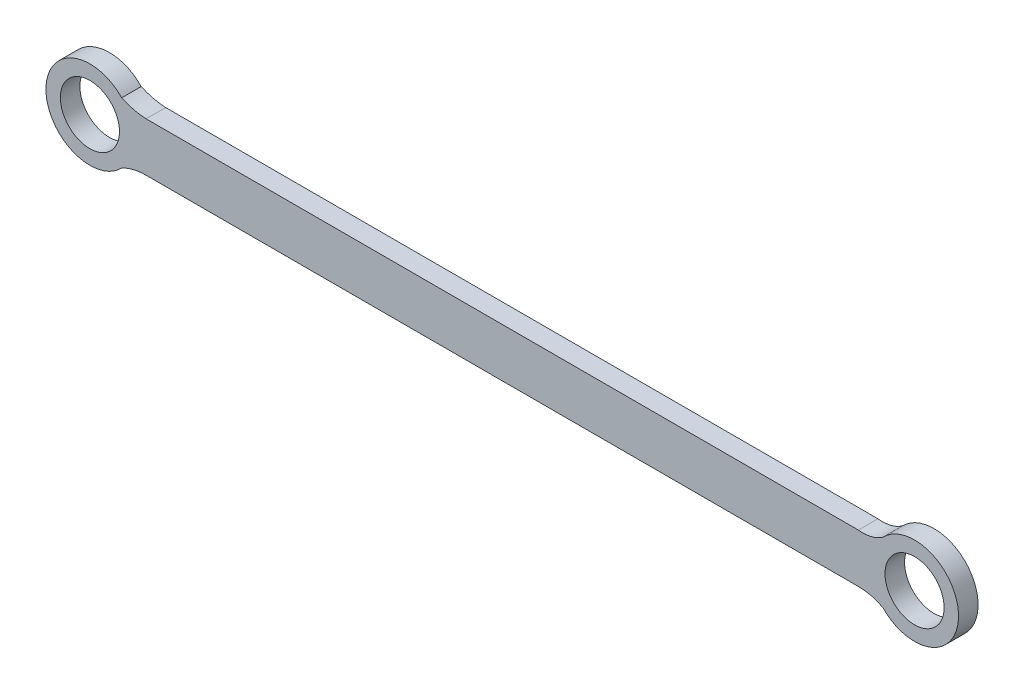
SolidWorks part; units mm, degrees
ref_plane "前视基准面" through (0, 0, 0) normal (0, 0, 1) x (1, 0, 0)
ref_plane "上视基准面" through (0, 0, 0) normal (0, 1, 0) x (1, 0, 0)
ref_plane "右视基准面" through (0, 0, 0) normal (1, 0, 0) x (0, 0, -1)
sketch "草图1" plane through (0, 0, 0) normal (0, 0, 1) x (1, 0, 0)
  line L0 (82, 4.5009) -> (-63.75, 4.5009)
  line L1 (-63.75, -5.4991) -> (82, -5.4991)
  line L2 (-141.9968, -0.4991) -> (145.6273, -0.4991) construction
  line L3 (0, 49.3748) -> (0, -44.6051) construction
  line L4 (93.4981, 49.3748) -> (93.4981, -44.6051) construction
  line L5 (-75.2519, 47.3518) -> (-75.2519, -43.3177) construction
  line L6 (82, 49.3748) -> (82, -47.6473) construction
  line L7 (-63.75, 55.807) -> (-63.75, -36.1499) construction
  line L8 (-68.75, 47.3518) -> (-68.75, -44.6276) construction
  line L9 (87, 49.3748) -> (87, -48.6816) construction
  circle A0 centre (-75.2519, -0.4991) radius 6.05
  circle A1 centre (93.4981, -0.4991) radius 6.05
  arc A2 (-68.75, 5.7239) -> (-63.75, 4.5009) centre (-63.154, 17.7701) ccw
  arc A3 (-68.75, 5.7239) -> (-68.75, -6.722) centre (-75.2519, -0.4991) ccw
  arc A4 (-63.75, -5.4991) -> (-68.75, -6.722) centre (-63.8572, -15.8933) ccw
  arc A5 (87, -6.726) -> (82, -5.4991) centre (82, -16.3005) ccw
  arc A6 (87, -6.726) -> (87, 5.7279) centre (93.4981, -0.4991) ccw
  arc A7 (82, 4.5009) -> (87, 5.7279) centre (82.9285, 11.5187) ccw
  dimension "D5" = 9
  dimension "D6" = 9
  dimension "D7" = 12.1
  dimension "D8" = 12.1
  dimension "D2" = 168.75
  dimension "D3" = 5
  dimension "D4" = 5
  dimension "D11" = 5
  dimension "D12" = 5
extrude "凸台-拉伸1" add sketch "草图1" along normal blind 4
